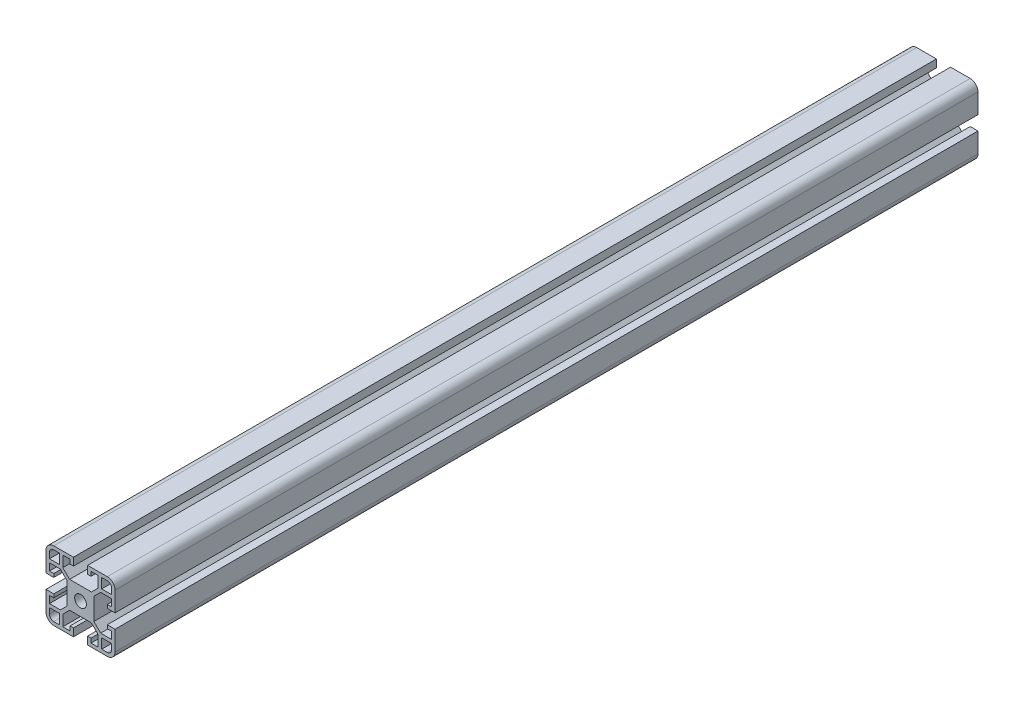
SolidWorks part; units mm, degrees
ref_plane "Front Plane" through (0, 0, 0) normal (0, 0, 1) x (1, 0, 0)
ref_plane "Top Plane" through (0, 0, 0) normal (0, 1, 0) x (1, 0, 0)
ref_plane "Right Plane" through (0, 0, 0) normal (1, 0, 0) x (0, 0, -1)
sketch "Sketch1" plane through (0, 0, 0) normal (0, 0, 1) x (1, 0, 0)
  circle B0 centre (0, 0) radius 3.4
  line B1 (7.75, -6.3358) -> (7.75, 6.3358)
  line B2 (7.75, 6.3358) -> (11.6642, 10.25)
  line B3 (11.6642, 10.25) -> (18, 10.25)
  line B4 (18, 10.25) -> (18, 6.1)
  line B5 (18, 6.1) -> (15.5, 6.1)
  line B6 (15.5, 6.1) -> (15.5, 4.1)
  line B7 (15.5, 4.1) -> (20, 4.1)
  line B8 (20, 4.1) -> (20, 15.5)
  arc B9 (20, 15.5) -> (15.5, 20) centre (15.5, 15.5) ccw
  line B10 (15.5, 20) -> (4.1, 20)
  line B11 (4.1, 20) -> (4.1, 15.5)
  line B12 (4.1, 15.5) -> (6.1, 15.5)
  line B13 (6.1, 15.5) -> (6.1, 18)
  line B14 (6.1, 18) -> (10.25, 18)
  line B15 (10.25, 18) -> (10.25, 11.6642)
  line B16 (10.25, 11.6642) -> (6.3358, 7.75)
  line B17 (6.3358, 7.75) -> (-6.3358, 7.75)
  line B18 (-10.25, 11.6642) -> (-6.3358, 7.75)
  line B19 (-10.25, 18) -> (-10.25, 11.6642)
  line B20 (-6.1, 18) -> (-10.25, 18)
  line B21 (-6.1, 15.5) -> (-6.1, 18)
  line B22 (-4.1, 15.5) -> (-6.1, 15.5)
  line B23 (-4.1, 20) -> (-4.1, 15.5)
  line B24 (-15.5, 20) -> (-4.1, 20)
  arc B25 (-15.5, 20) -> (-20, 15.5) centre (-15.5, 15.5) ccw
  line B26 (-20, 4.1) -> (-20, 15.5)
  line B27 (-15.5, 4.1) -> (-20, 4.1)
  line B28 (-15.5, 6.1) -> (-15.5, 4.1)
  line B29 (-18, 6.1) -> (-15.5, 6.1)
  line B30 (-18, 10.25) -> (-18, 6.1)
  line B31 (-11.6642, 10.25) -> (-18, 10.25)
  line B32 (-7.75, 6.3358) -> (-11.6642, 10.25)
  line B33 (-7.75, -6.3358) -> (-7.75, 6.3358)
  line B34 (-7.75, -6.3358) -> (-11.6642, -10.25)
  line B35 (-11.6642, -10.25) -> (-18, -10.25)
  line B36 (-18, -10.25) -> (-18, -6.1)
  line B37 (-18, -6.1) -> (-15.5, -6.1)
  line B38 (-15.5, -6.1) -> (-15.5, -4.1)
  line B39 (-15.5, -4.1) -> (-20, -4.1)
  line B40 (-20, -4.1) -> (-20, -15.5)
  arc B41 (-20, -15.5) -> (-15.5, -20) centre (-15.5, -15.5) ccw
  line B42 (-15.5, -20) -> (-4.1, -20)
  line B43 (-4.1, -20) -> (-4.1, -15.5)
  line B44 (-4.1, -15.5) -> (-6.1, -15.5)
  line B45 (-6.1, -15.5) -> (-6.1, -18)
  line B46 (-6.1, -18) -> (-10.25, -18)
  line B47 (-10.25, -18) -> (-10.25, -11.6642)
  line B48 (-10.25, -11.6642) -> (-6.3358, -7.75)
  line B49 (6.3358, -7.75) -> (-6.3358, -7.75)
  line B50 (10.25, -11.6642) -> (6.3358, -7.75)
  line B51 (10.25, -18) -> (10.25, -11.6642)
  line B52 (6.1, -18) -> (10.25, -18)
  line B53 (6.1, -15.5) -> (6.1, -18)
  line B54 (4.1, -15.5) -> (6.1, -15.5)
  line B55 (4.1, -20) -> (4.1, -15.5)
  line B56 (15.5, -20) -> (4.1, -20)
  arc B57 (15.5, -20) -> (20, -15.5) centre (15.5, -15.5) ccw
  line B58 (20, -4.1) -> (20, -15.5)
  line B59 (15.5, -4.1) -> (20, -4.1)
  line B60 (15.5, -6.1) -> (15.5, -4.1)
  line B61 (18, -6.1) -> (15.5, -6.1)
  line B62 (18, -10.25) -> (18, -6.1)
  line B63 (11.6642, -10.25) -> (18, -10.25)
  line B64 (7.75, -6.3358) -> (11.6642, -10.25)
  line B65 (15.5, 18) -> (12.25, 18)
  line B66 (12.25, 18) -> (12.25, 12.25)
  line B67 (12.25, 12.25) -> (18, 12.25)
  line B68 (18, 12.25) -> (18, 15.5)
  arc B69 (18, 15.5) -> (15.5, 18) centre (15.5, 15.5) ccw
  line B70 (-15.5, 18) -> (-12.25, 18)
  line B71 (-12.25, 18) -> (-12.25, 12.25)
  line B72 (-12.25, 12.25) -> (-18, 12.25)
  line B73 (-18, 12.25) -> (-18, 15.5)
  arc B74 (-15.5, 18) -> (-18, 15.5) centre (-15.5, 15.5) ccw
  line B75 (-15.5, -18) -> (-12.25, -18)
  line B76 (-12.25, -18) -> (-12.25, -12.25)
  line B77 (-12.25, -12.25) -> (-18, -12.25)
  line B78 (-18, -12.25) -> (-18, -15.5)
  arc B79 (-18, -15.5) -> (-15.5, -18) centre (-15.5, -15.5) ccw
  line B80 (15.5, -18) -> (12.25, -18)
  line B81 (12.25, -18) -> (12.25, -12.25)
  line B82 (12.25, -12.25) -> (18, -12.25)
  line B83 (18, -12.25) -> (18, -15.5)
  arc B84 (15.5, -18) -> (18, -15.5) centre (15.5, -15.5) ccw
sketch_block_instance "S8-4040 - H-1"
sketch_block "S8-4040 - H"
extrude "Boss-Extrude1" add sketch "Sketch1" along normal blind 500
